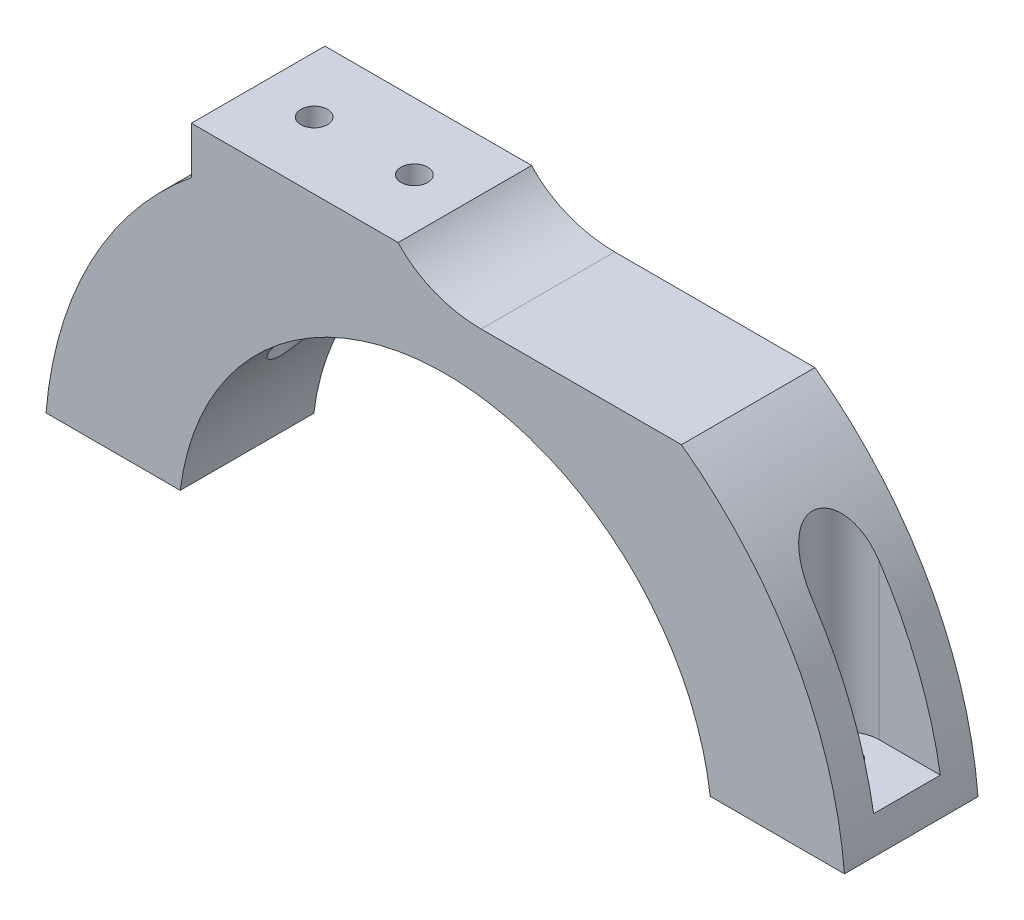
SolidWorks part; units mm, degrees
ref_plane "Front Plane" through (0, 0, 0) normal (0, 0, 1) x (1, 0, 0)
ref_plane "Top Plane" through (0, 0, 0) normal (0, 1, 0) x (1, 0, 0)
ref_plane "Right Plane" through (0, 0, 0) normal (1, 0, 0) x (0, 0, -1)
sketch "Sketch1" plane through (0, 0, 0) normal (0, 0, 1) x (1, 0, 0)
  line L1 (-40, 0) -> (-60, 0)
  line L4 (0, 48.4615) -> (0, 0) construction
  line L5 (0, 48.4615) -> (0, 40)
  line L7 (-35.3763, 48.4615) -> (0, 48.4615)
  arc A0 (0, 40) -> (-40, 0) centre (0, 0) ccw
  arc A5 (-35.3763, 48.4615) -> (-60, 0) centre (0, 0) ccw
  dimension "D1" = 40
  dimension "D2" = 20
extrude "Boss-Extrude1" add sketch "Sketch1" along normal blind 20
sketch "Sketch2" plane through (0, 0, 0) normal (0, -1, 0) x (1, 0, 0)
  line L0 (-60, 20) -> (-60, 0) construction
  line L3 (-40, 0) -> (-60, 0) construction
  circle A0 centre (-50, 10) radius 2.25
  dimension "D1" = 10
  dimension "D3" = 4.5
  dimension "D2" = 10
extrude "Cut-Extrude1" cut sketch "Sketch2" against normal blind 79
sketch "Sketch6" plane through (0, 0, 0) normal (0, -1, 0) x (1, 0, 0)
  line L0 (-60, 20) -> (-60, 0) construction
  line L1 (-50, 5) -> (-60, 5)
  line L2 (-50, 5) -> (-50, 15)
  line L3 (-50, 15) -> (-60, 15)
  line L4 (-60, 5) -> (-60, 15)
  circle A0 centre (-50, 10) radius 5
  circle M5 centre (-50, 10) radius 2.25
  line M9 (-60, 20) -> (-60, 0)
extrude "Cut-Extrude4" cut sketch "Sketch6" against normal blind 59 contours A0 L3 L1 M9 | L2 A0 M5 | L2 A0 M5
sketch "Sketch7" plane through (0, 0, 0) normal (0, -1, 0) x (1, 0, 0)
  line L0 (-50, 15) -> (-60, 15)
  line L1 (-60, 15) -> (-60, 5)
  line L2 (-60, 5) -> (-50, 5)
  arc A0 (-50, 5) -> (-50, 15) centre (-50, 10) ccw
  circle A1 centre (-50, 10) radius 2
extrude "Boss-Extrude3" add sketch "Sketch7" against normal blind 10
sketch "Sketch8" plane through (0, 0, 20) normal (0, 0, 1) x (1, 0, 0)
  line L0 (-57, 0) -> (-64.996, 0)
  line L1 (-64.996, 0) -> (-57, 0)
  line L2 (-55.4021, 13.4017) -> (-63.174, 15.2817)
  arc A0 (-55.4021, 13.4017) -> (-57, 0) centre (0, 0) ccw
  arc A1 (-63.174, 15.2817) -> (-64.996, 0) centre (0, 0) ccw
  arc M2 (-35.3763, 48.4615) -> (-60, 0) centre (0, 0) ccw
  dimension "D4" = 57
  dimension "D1" = 7.996
  dimension "D2" = 7.996
  dimension "D3" = 13.599
extrude "Cut-Extrude5" cut sketch "Sketch8" against normal blind 23 contours L2 A1 L0 M2
mirror "Mirror1" about plane through (0, 0, 20) normal (1, 0, 0) of "Cut-Extrude5", "Cut-Extrude4", "Cut-Extrude1", "Boss-Extrude1", "Boss-Extrude3"
sketch "Sketch3" plane through (0, 0, 0) normal (0, 0, -1) x (-1, 0, 0)
  line L0 (-5.3763, 66.1615) -> (-5.3763, 53.4615)
  line L1 (35.3763, 48.4615) -> (-5.3763, 48.4615)
  line L4 (-5.3763, 48.4615) -> (-5.3763, 71.1615)
  line L5 (-5.3763, 66.1615) -> (-5.3763, 53.4615)
  line L6 (-5.3763, 66.1615) -> (34.6237, 66.1615)
  line L7 (-5.3763, 53.4615) -> (34.6237, 53.4615)
  line L8 (34.6237, 66.1615) -> (34.6237, 53.4615)
  line L9 (34.6237, 53.4615) -> (38.0164, 53.4615)
  line L10 (34.6237, 53.4615) -> (34.6237, 49.002)
  line L11 (35.3763, 48.4615) -> (-5.3763, 48.4615)
  line L12 (35.3763, 48.4615) -> (-5.3763, 48.4615)
  line L13 (38.0164, 53.4615) -> (38.0164, 46.4193)
  line L14 (34.6237, 49.002) -> (38.0164, 46.4193)
  line L16 (34.6237, 66.1615) -> (-5.3763, 66.1615)
  line L18 (35.3763, 48.4615) -> (-5.3763, 48.4615)
  line L19 (-5.3763, 66.1615) -> (-5.3763, 48.4615)
  arc A0 (35.3763, 48.4615) -> (50.3988, 32.557) centre (0, 0) cw
  arc A1 (60, 0) -> (35.3763, 48.4615) centre (0, 0) ccw construction
  ellipse E0 centre (-5.3763, 59.8115) end of major axis (9.6237, 59.8115) minor radius 11.35
  dimension "D1" = 12.7
  dimension "D2" = 40
  dimension "D3" = 5
  dimension "D4" = 70
extrude "Boss-Extrude2" add sketch "Sketch3" against normal blind 20
sketch "Sketch4" plane through (0, 53.4615, 0) normal (0, 1, 0) x (1, 0, 0)
  line L0 (5.3763, -20) -> (5.3763, 0) construction
  line L2 (-34.6237, 0) -> (-34.6237, -20)
  line L3 (-34.6237, -20) -> (-7.0565, -20)
  line L4 (-7.0565, 0) -> (-7.0565, -20)
  circle A0 centre (-29.6237, -10) radius 2.25
  circle A1 centre (-14.6237, -10) radius 2.25
  dimension "D1" = 5
  dimension "D2" = 15
  dimension "D3" = 4.5
  dimension "D4" = 4.5
  dimension "D5" = 40
extrude "Cut-Extrude2" cut sketch "Sketch4" against normal blind 30 contours A0 | A1
sketch "Sketch9" plane through (0, 53.4615, 0) normal (0, 1, 0) x (1, 0, 0)
  line L0 (-29.6237, -5) -> (-14.6237, -5)
  line L1 (-14.6237, -15) -> (-29.6237, -15)
  arc A0 (-29.6237, -5) -> (-29.6237, -15) centre (-29.6237, -10) ccw
  arc A1 (-14.6237, -15) -> (-14.6237, -5) centre (-14.6237, -10) ccw
  dimension "D1" = 5
extrude "Cut-Extrude6" cut sketch "Sketch9" against normal blind 36
sketch "Sketch10" plane through (0, 53.4615, 0) normal (0, 1, 0) x (1, 0, 0)
  line L0 (-29.6237, -5) -> (-14.6237, -5)
  line L1 (-29.6237, -15) -> (-14.6237, -15)
  arc A0 (-29.6237, -5) -> (-29.6237, -15) centre (-29.6237, -10) ccw
  arc A1 (-14.6237, -15) -> (-14.6237, -5) centre (-14.6237, -10) ccw
  circle A2 centre (-29.6237, -10) radius 2
  circle A3 centre (-14.6237, -10) radius 2
extrude "Boss-Extrude4" add sketch "Sketch10" against normal blind 5
sketch "Sketch12" plane through (0, 0, 0) normal (0, 0, -1) x (-1, 0, 0)
  line L0 (-60, 0) -> (60, 0)
  line L1 (-60, 0) -> (-60, 5)
  line L2 (60, 0) -> (60, 5)
  line L3 (-60, 5) -> (60, 5)
  dimension "D1" = 5
extrude "Cut-Extrude7" cut sketch "Sketch12" against normal blind 20
